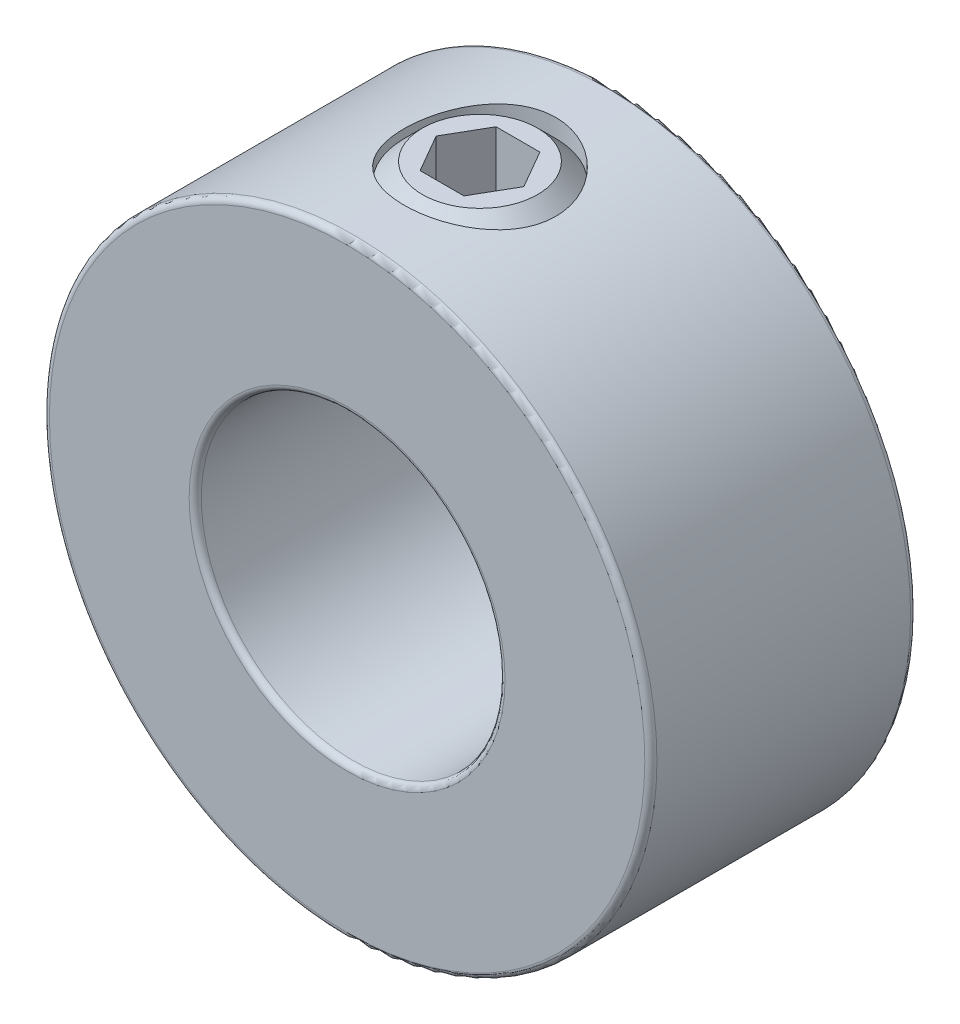
SolidWorks part; units mm, degrees
ref_plane "Front Plane" through (0, 0, 0) normal (0, 0, 1) x (1, 0, 0)
ref_plane "Top Plane" through (0, 0, 0) normal (0, 1, 0) x (1, 0, 0)
ref_plane "Right Plane" through (0, 0, 0) normal (1, 0, 0) x (0, 0, -1)
sketch "Sketch1" plane through (0, 0, 0) normal (0, 0, 1) x (1, 0, 0)
  circle A0 centre (0, 0) radius 12.7
  circle A1 centre (0, 0) radius 6.35
  point P4 (12.7, 0)
  dimension "Bore Dia" = 12.7
  dimension "OD" = 25.4
extrude "Extrude1" add sketch "Sketch1" along normal mid plane 11.1125
sketch "Sketch2" plane through (41.275, 0, 0) normal (0, -1, 0) x (0, 0, -1)
  line L0 (5.5562, -41.275) -> (-5.5563, -41.275) construction
  line L1 (-5.5562, -28.575) -> (-5.5562, -53.975) construction
  line L2 (5.5562, -53.975) -> (5.5562, -28.575) construction
  circle A0 centre (0, -41.275) radius 3.175
  point P7 (0, -44.45)
  dimension "Set Screw Dia" = 6.35
extrude "Cut-Extrude1" cut sketch "Sketch2" against normal through all
fillet "Fillet1" radius 0.254 4 edges at (6.35, 0, -5.5562) (6.35, 0, 5.5562) (12.7, 0, -5.5562) (12.7, 0, 5.5562)
sketch "Sketch3" plane through (0, 0, 0) normal (0, 0, 1) x (1, 0, 0)
  line L0 (-2.4082, 6.35) -> (-0.9202, 6.35)
  line L1 (0, 7.2702) -> (-0.9202, 6.35)
  line L2 (0, 7.2702) -> (0, 12.7)
  line L3 (0, 12.7) -> (-2.4082, 12.7)
  line L4 (-3.175, 7.1168) -> (-3.175, 11.9332)
  line L5 (0, 6.35) -> (0, 0) construction
  line L6 (-3.175, 7.1168) -> (-3.175, 6.35) construction
  line L7 (-3.175, 6.35) -> (-2.4082, 6.35) construction
  line L8 (-3.175, 11.9332) -> (-3.175, 12.7) construction
  line L9 (-2.4082, 6.35) -> (-3.175, 7.1168)
  line L10 (-3.175, 11.9332) -> (-2.4082, 12.7)
  line L11 (-3.175, 12.7) -> (-2.4082, 12.7) construction
  line L12 (-0.9202, 6.35) -> (0, 6.35) construction
  line L13 (0, 6.35) -> (0, 7.2702) construction
  circle A1 centre (0, 0) radius 6.35 construction
  dimension "D1" = 0.9202
  dimension "D2" = 0.7668
  dimension "Screw Length" = 6.35
revolve "Revolve1" add sketch "Sketch3" angle 360 about L5
sketch "Sketch4" plane through (3.3734, 12.7, 0) normal (0, -1, 0) x (0, 0, -1)
  line L1 (0, -1.5404) -> (-1.5875, -2.4569)
  line L2 (-1.5875, -2.4569) -> (-1.5875, -4.29)
  line L3 (-1.5875, -4.29) -> (0, -5.2065)
  line L4 (0, -5.2065) -> (1.5875, -4.29)
  line L5 (1.5875, -4.29) -> (1.5875, -2.4569)
  line L6 (1.5875, -2.4569) -> (0, -1.5404)
  circle A0 centre (0, -3.3734) radius 1.5875 construction
  circle A1 centre (0, -3.3734) radius 1.8331 construction
  dimension "D1" = 3.6662
  dimension "Hex Size" = 3.175
extrude "Cut-Extrude2" cut sketch "Sketch4" along normal blind 3.175
equation "\"D1@Fillet1\" = \"OD@Sketch1\"*.01"
equation "\"D1@Cut-Extrude2\" = \"Hex Size@Sketch4\""
equation "\"D2@Sketch3\" =(\"Set Screw Dia@Sketch2\"-\"D1@Sketch4\")/3.5"
equation "\"D1@Sketch3\" = \"D2@Sketch3\"*1.2"
